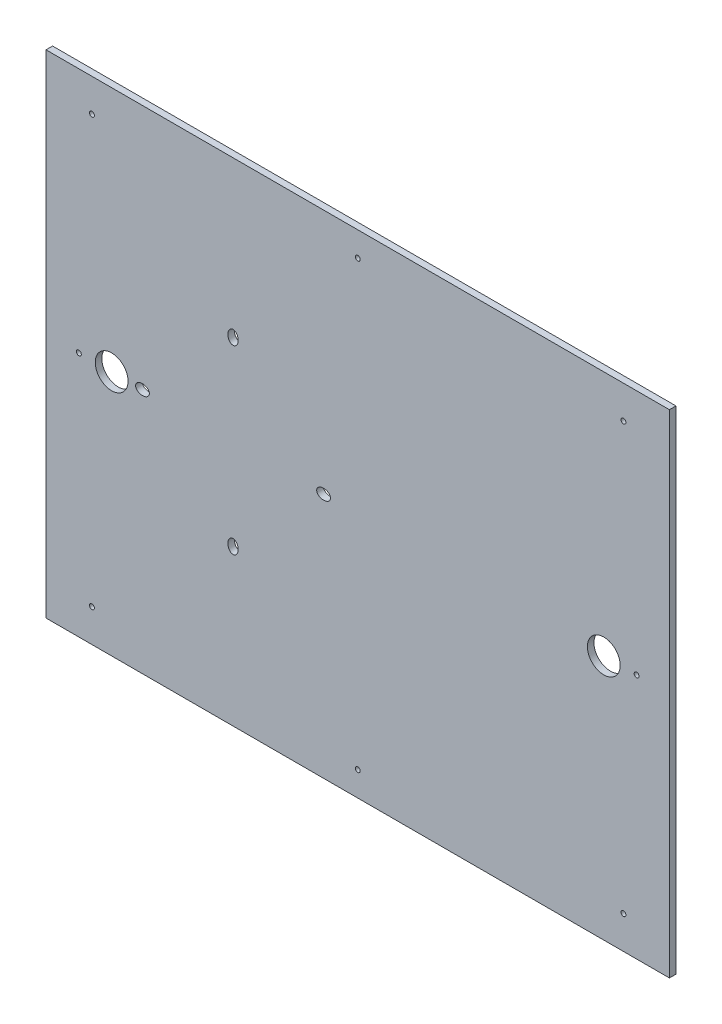
SolidWorks part; units mm, degrees
ref_plane "Front Plane" through (0, 0, 0) normal (0, 0, 1) x (1, 0, 0)
ref_plane "Top Plane" through (0, 0, 0) normal (0, 1, 0) x (1, 0, 0)
ref_plane "Right Plane" through (0, 0, 0) normal (1, 0, 0) x (0, 0, -1)
sketch "Sketch3" plane through (0, 0, 0) normal (0, 0, 1) x (1, 0, 0)
  line L0 (-313.1499, 197.7637) -> (66.8501, 197.7637)
  line L1 (66.8501, 197.7637) -> (66.8501, -102.2363)
  line L2 (66.8501, -102.2363) -> (-313.1499, -102.2363)
  line L3 (-313.1499, -102.2363) -> (-313.1499, 197.7637)
extrude "Boss-Extrude1" add sketch "Sketch3" along normal blind 4
hole_wizard "Hole2" positions "3DSketch4" profile "Sketch7" legacy
sketch3d "3DSketch4"
  line L0 (-313.1499, 197.7637, 4) -> (-313.1499, -102.2363, 4) construction
  line L1 (66.8501, 197.7637, 4) -> (-313.1499, 197.7637, 4) construction
  line L2 (66.8501, -102.2363, 4) -> (66.8501, 197.7637, 4) construction
  point P0 (-273.1499, 47.7637, 4)
  point P2 (26.8501, 47.7637, 4)
  dimension "D1" = 40
  dimension "D2" = 150
  dimension "D3" = 150
  dimension "D4" = 40
sketch "Sketch7" plane through (-273.1499, 47.7637, 4) normal (1, 0, 0) x (0, -1, 0)
  line L0 (0, 0) -> (0, 100)
  line L1 (0, 100) -> (10, 100)
  line L2 (10, 100) -> (10, 0)
  line L3 (10, 0) -> (0, 0)
  line L4 (0, 110) -> (0, -10) construction
  dimension "Diameter" = 20
  dimension "Depth" = 100
sketch "Sketch10" plane through (0, 0, 0) normal (0, 0, -1) x (-1, 0, 0)
  circle A0 centre (285.1499, 177.7637) radius 1.5
  circle A10 centre (-38.8501, 177.7637) radius 1.5
  circle A15 centre (-38.8501, -82.2363) radius 1.5
  circle A20 centre (285.1499, -82.2363) radius 1.5
  dimension "D5" = 2
  dimension "D6" = 2
extrude "Cut-Extrude1" cut sketch "Sketch10" against normal blind 4
sketch "Sketch11" plane through (0, 0, 0) normal (0, 0, -1) x (-1, 0, 0)
  circle A3 centre (293.1499, 47.7637) radius 1.5
  circle A7 centre (123.1499, 182.7637) radius 1.5
  circle A8 centre (-46.8501, 47.7637) radius 1.5
  circle A10 centre (123.1499, -87.2363) radius 1.5
extrude "Cut-Extrude2" cut sketch "Sketch11" against normal blind 4
sketch "Sketch12" plane through (0, 0, 0) normal (0, 0, -1) x (-1, 0, 0)
  ellipse E0 centre (199.1499, -7.4363) end of major axis (199.1499, -3.2363) minor radius 3.15
  ellipse E1 centre (143.9499, 47.7637) end of major axis (148.1499, 47.7637) minor radius 3.15
  ellipse E2 centre (199.1499, 102.9637) end of major axis (199.1499, 98.7637) minor radius 3.15
  ellipse E3 centre (254.3499, 47.7637) end of major axis (250.1499, 47.7637) minor radius 3.15
  point P33 (199.1499, 47.7637)
extrude "Cut-Extrude9" cut sketch "Sketch12" against normal blind 4
